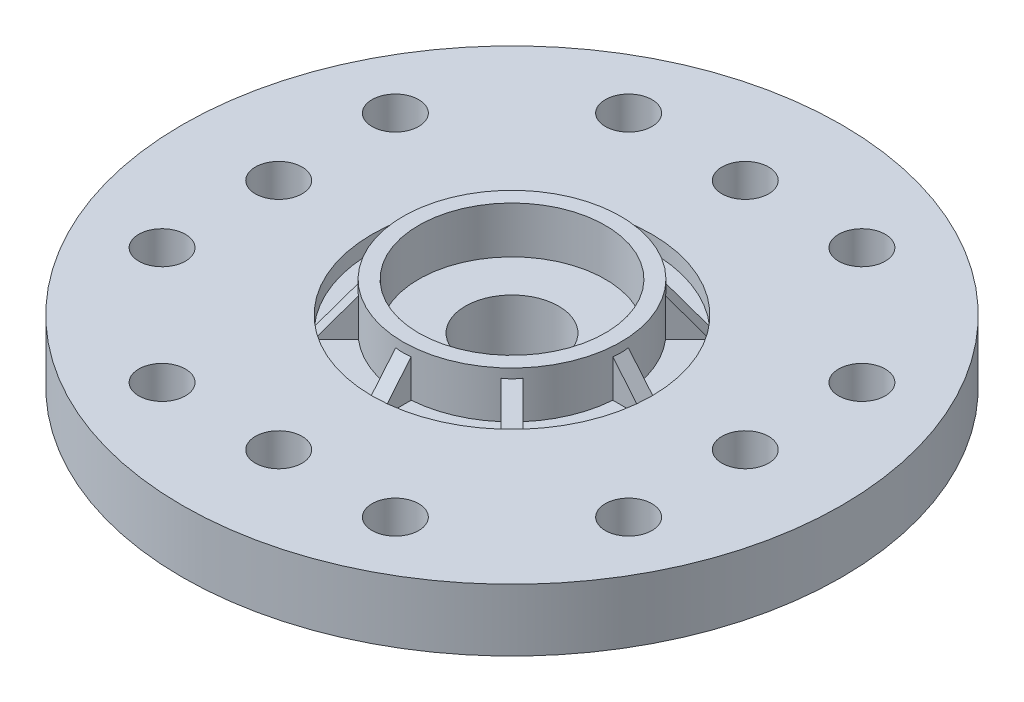
SolidWorks part; units mm, degrees
ref_plane "Front Plane" through (0, 0, 0) normal (0, 0, 1) x (1, 0, 0)
ref_plane "Top Plane" through (0, 0, 0) normal (0, 1, 0) x (1, 0, 0)
ref_plane "Right Plane" through (0, 0, 0) normal (1, 0, 0) x (0, 0, -1)
sketch "Sketch1" plane through (0, 0, 0) normal (0, 1, 0) x (1, 0, 0)
  circle A0 centre (0, 0) radius 10.6
  dimension "D1" = 21.2
extrude "Boss-Extrude1" add sketch "Sketch1" along normal blind 2
sketch "Sketch2" plane through (0, 0, 0) normal (0, 1, 0) x (1, 0, 0)
  line L0 (-3.75, 7.5) -> (3.75, 7.5) construction
  circle A0 centre (-3.75, 7.5) radius 0.75
  circle A1 centre (3.75, 7.5) radius 0.75
  circle A2 centre (0, 7.5) radius 0.75
  point P2 (0, 7.5)
  dimension "D1" = 1.5
  dimension "D2" = 7.5
  dimension "D3" = 7.5
extrude "Cut-Extrude2" cut sketch "Sketch2" along normal through all
pattern_circular "CirPattern1" count 4 over 360 about axis through (0, 0, 0) along (0, 1, 0) of "Cut-Extrude2"
sketch "Sketch3" plane through (0, 0, 0) normal (0, -1, 0) x (1, 0, 0)
  circle A0 centre (0, 0) radius 3.85
  dimension "D1" = 7.7
extrude "Boss-Extrude2" add sketch "Sketch3" along normal blind 4.5
sketch "Sketch4" plane through (0, -4.5, 0) normal (0, -1, 0) x (1, 0, 0)
  circle A0 centre (0, 0) radius 3
  dimension "D1" = 6
extrude "Cut-Extrude3" cut sketch "Sketch4" against normal blind 3.5
sketch "Sketch5" plane through (0, -1, 0) normal (0, -1, 0) x (1, 0, 0)
  circle A0 centre (0, 0) radius 1.5
  dimension "D1" = 3
extrude "Cut-Extrude4" cut sketch "Sketch5" against normal through all
fillet "Fillet1" radius 1 1 edges at (0, 0, 3.85)
sketch "Sketch6" plane through (0, 2, 0) normal (0, 1, 0) x (1, 0, 0)
  circle A0 centre (0, 0) radius 4.5
  dimension "D1" = 9
extrude "Cut-Extrude5" cut sketch "Sketch6" against normal blind 0.5
sketch "Sketch7" plane through (0, 1.5, 0) normal (0, 1, 0) x (1, 0, 0)
  circle A0 centre (0, 0) radius 3.5
  circle A1 centre (0, 0) radius 3
  dimension "D1" = 7
  dimension "D2" = 0.5
extrude "Boss-Extrude3" add sketch "Sketch7" along normal blind 1.5
sketch "Sketch8" plane through (0, 0, 0) normal (1, 0, 0) x (0, 0, -1)
  line L0 (-4.5, 1.5) -> (-3, 1.5)
  line L1 (-3, 1.5) -> (-3, 3)
  line L2 (-4.5, 1.5) -> (-3.25, 3)
  line L3 (-3.25, 3) -> (-3, 3)
  dimension "D1" = 0.25
extrude "Boss-Extrude4" add sketch "Sketch8" along normal mid plane 0.5
pattern_circular "CirPattern2" count 8 over 360 about axis through (0, 0, 0) along (0, 1, 0) of "Boss-Extrude4"
